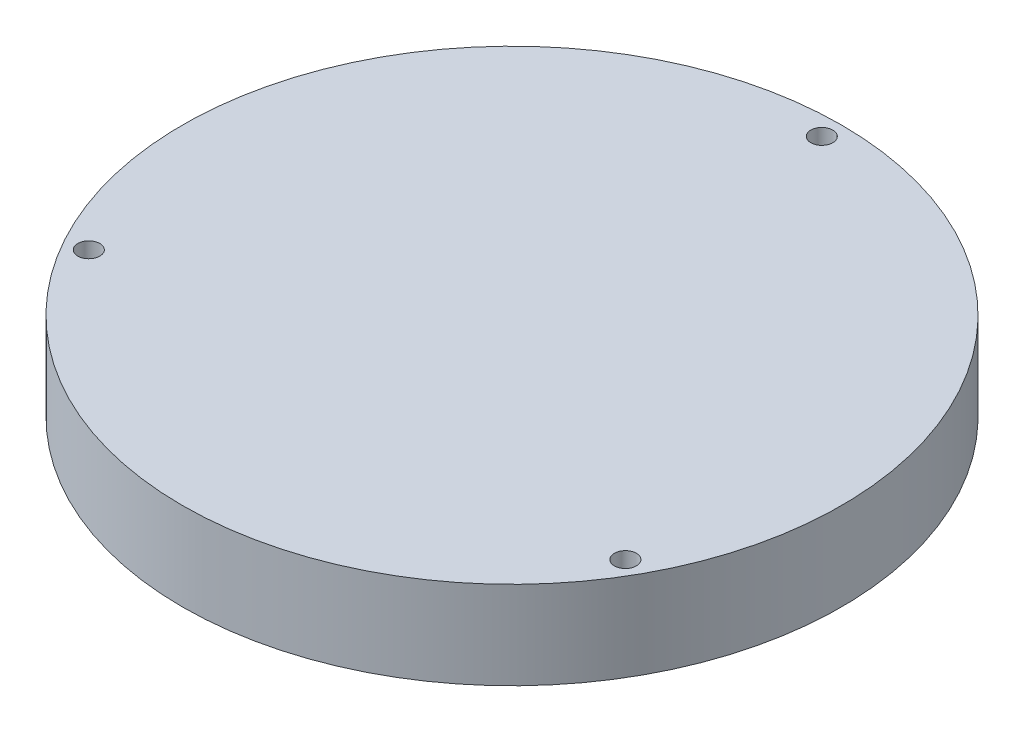
SolidWorks part; units mm, degrees
ref_plane "Front Plane" through (0, 0, 0) normal (0, 0, 1) x (1, 0, 0)
ref_plane "Top Plane" through (0, 0, 0) normal (0, 1, 0) x (1, 0, 0)
ref_plane "Right Plane" through (0, 0, 0) normal (1, 0, 0) x (0, 0, -1)
sketch "Sketch1" plane through (0, 0, 0) normal (0, 1, 0) x (1, 0, 0)
  circle A0 centre (0, 0) radius 95.25
  dimension "D1" = 190.5
extrude "Boss-Extrude1" add sketch "Sketch1" along normal mid plane 25.4
sketch "Sketch2" plane through (0, 12.7, 0) normal (0, 1, 0) x (1, 0, 0)
  line L0 (0, 0) -> (0, 109.4687) construction
  line L1 (0, 0) -> (96.8035, 55.8895) construction
  circle A0 centre (0, 0) radius 89.535 construction
  circle A1 centre (0, 0) radius 95.25 construction
  circle A2 centre (0, 89.535) radius 3.175
  point P9 (0, 0)
  dimension "D1" = 5.715
  dimension "D3" = 6.35
  dimension "D2" = 60
extrude "Cut-Extrude1" cut sketch "Sketch2" against normal through all
pattern_circular "CirPattern1" count 3 over 360 about axis through (0, 0, 0) along (0, 1, 0) of "Cut-Extrude1"
sketch "Sketch3" plane through (0, -12.7, 0) normal (0, -1, 0) x (-1, 0, 0)
  line L0 (0, 0) -> (-96.8035, 55.8895) construction
  circle A0 centre (-77.5396, 44.7675) radius 2.8448
  circle A1 centre (0, 0) radius 89.535 construction
  point P6 (0, 0)
  dimension "D1" = 5.6896
extrude "Cut-Extrude2" cut sketch "Sketch3" against normal up to surface (12.7 mm away) up to plane "Top Plane"
pattern_circular "CirPattern2" count 3 over 360 about axis through (0, 0, 0) along (0, 1, 0) of "Cut-Extrude2"
